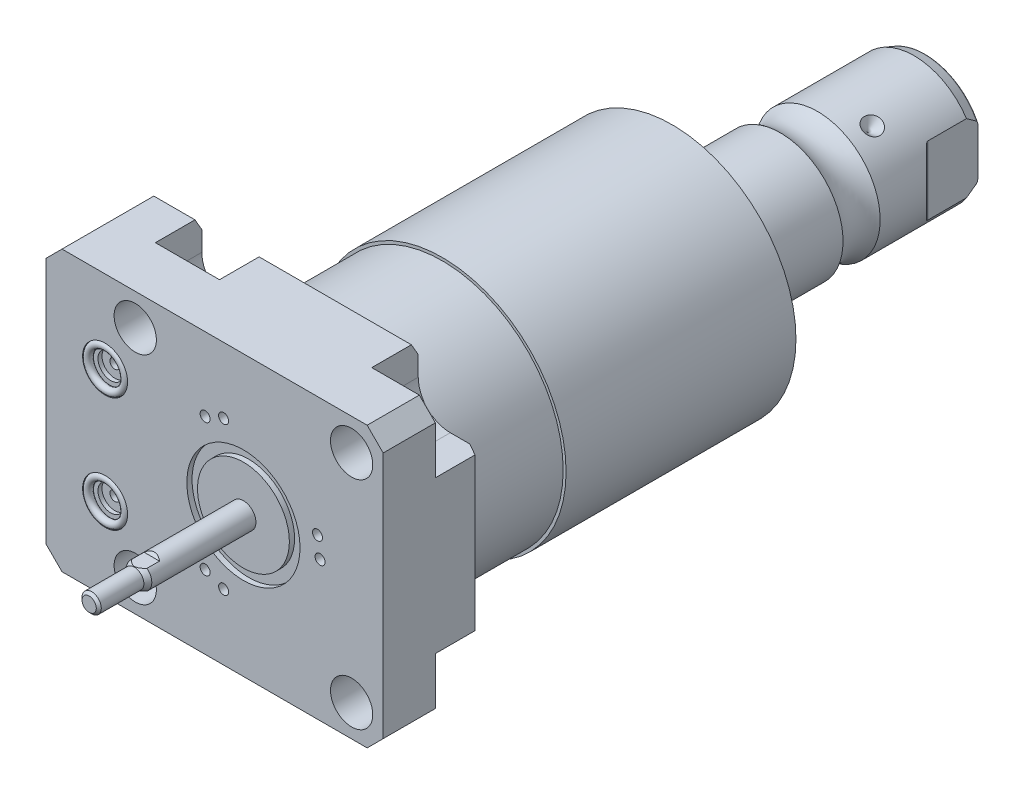
SolidWorks part; units mm, degrees
material "Alloy Steel"
ref_plane "Front Plane" through (0, 0, 0) normal (0, 0, 1) x (1, 0, 0)
ref_plane "Top Plane" through (0, 0, 0) normal (0, 1, 0) x (1, 0, 0)
ref_plane "Right Plane" through (0, 0, 0) normal (1, 0, 0) x (0, 0, -1)
sketch "Sketch1" plane through (0, 0, 0) normal (0, 0, 1) x (1, 0, 0)
  line L0 (-50.063, 35.433) -> (35.433, 35.433)
  line L1 (35.433, 35.433) -> (35.433, -35.433)
  line L2 (35.433, -35.433) -> (-50.063, -35.433)
  line L3 (-50.063, -35.433) -> (-50.063, 35.433)
  dimension "D1" = 85.496
  dimension "D2" = 70.866
  dimension "D3" = 35.433
  dimension "D4" = 35.433
extrude "Extrude1" add sketch "Sketch1" along normal blind 25.019
hole_wizard "Hole1" positions "Sketch22" profile "Sketch21" legacy end condition through all
sketch "Sketch22" plane through (0, 0, 0) normal (0, 0, -1) x (-1, 0, 0)
  line L0 (0, 0) -> (42.7441, 0) construction
  line L1 (0, 0.8532) -> (0, 27.5062) construction
  point P0 (-27.432, -27.432)
  point P9 (-27.432, 27.432)
  point P11 (27.432, 27.432)
  point P12 (27.432, -27.432)
  dimension "D1" = 27.432
  dimension "D2" = 27.432
sketch "Sketch21" plane through (27.432, -27.432, 0) normal (1, 0, 0) x (0, 1, 0)
  line L0 (0, 0) -> (0, 25.019)
  line L1 (0, 25.019) -> (5.3595, 25.019)
  line L2 (5.3595, 25.019) -> (5.3595, 0)
  line L3 (5.3595, 0) -> (0, 0)
  line L4 (0, 110) -> (0, -10) construction
  dimension "Diameter" = 10.719
  dimension "Depth" = 25.019
sketch "Sketch3" plane through (0, 0, 0) normal (0, 0, -1) x (-1, 0, 0)
  line L0 (-27.432, -19.304) -> (-35.433, -19.304)
  line L1 (-35.433, -35.433) -> (-35.433, -19.304)
  line L2 (-35.433, 19.304) -> (-35.433, 35.433)
  line L3 (-35.433, 19.304) -> (-27.432, 19.304)
  line L4 (-19.304, 27.432) -> (-19.304, 35.433)
  line L5 (-35.433, 35.433) -> (-19.304, 35.433)
  line L6 (19.304, 35.433) -> (19.304, 27.432)
  line L7 (35.56, 27.432) -> (35.56, 35.433)
  line L8 (19.304, 35.433) -> (35.56, 35.433)
  line L9 (35.56, -35.433) -> (19.304, -35.433)
  line L10 (35.56, -35.433) -> (35.56, -27.432)
  line L11 (19.304, -27.432) -> (19.304, -35.433)
  line L12 (-19.304, -35.433) -> (-35.433, -35.433)
  line L13 (-19.304, -35.433) -> (-19.304, -27.432)
  line L14 (-35.433, 35.433) -> (50.063, 35.433) construction
  line L15 (-35.433, -35.433) -> (-35.433, 35.433) construction
  line L16 (50.063, -35.433) -> (-35.433, -35.433) construction
  arc A0 (-19.304, -27.432) -> (-27.432, -19.304) centre (-27.432, -27.432) ccw
  arc A1 (-27.432, 19.304) -> (-19.304, 27.432) centre (-27.432, 27.432) ccw
  arc A2 (19.304, 27.432) -> (35.56, 27.432) centre (27.432, 27.432) ccw
  arc A3 (35.56, -27.432) -> (19.304, -27.432) centre (27.432, -27.432) ccw
  circle A8 centre (-27.432, 27.432) radius 5.3595 construction
  circle A9 centre (-27.432, -27.432) radius 5.3595 construction
  circle A10 centre (27.432, -27.432) radius 5.3595 construction
  circle A11 centre (27.432, 27.432) radius 5.3595 construction
  dimension "D1" = 8.128
extrude "Cut-Extrude2" cut sketch "Sketch3" against normal blind 11.786
ref_plane "Plane16" through (0, 0, 12.522) normal (0, 0, 1) x (1, 0, 0)
sketch "Sketch23" plane through (0, 0, 12.522) normal (0, 0, 1) x (1, 0, 0)
  line L0 (-11.9397, -13.0048) -> (-61.0013, -13.0048) construction
  line L1 (-50.063, -23.749) -> (-49.809, -23.749)
  line L3 (-49.809, -23.749) -> (-49.809, -19.6596)
  line L4 (-49.809, -19.6596) -> (-49.0978, -18.9484)
  line L5 (-49.0978, -18.9484) -> (-35.6358, -18.9484)
  line L6 (-35.6358, -18.9484) -> (-35.6358, -13.0048)
  line L7 (-35.6358, -13.0048) -> (-50.063, -13.0048)
  line L8 (-50.063, -13.0048) -> (-50.063, -23.749)
  line L10 (-50.063, 35.433) -> (-50.063, -35.433) construction
  dimension "D1" = 21.4884
  dimension "D2" = 0.254
  dimension "D3" = 45
  dimension "D4" = 13.3096
  dimension "D5" = 11.8872
  dimension "D6" = 14.1732
  dimension "D7" = 13.0048
revolve "Cut-Revolve5" cut sketch "Sketch23" angle 360 about L0
mirror "Mirror1" about plane through (0, 0, 0) normal (0, 1, 0) of "Cut-Revolve5"
sketch "Sketch6" plane through (0, 0, 25.019) normal (0, 0, 1) x (1, 0, 0)
  line L0 (0, 0) -> (-71.0417, 0) construction
  circle A0 centre (-35.077, -14.529) radius 5.7023
  circle A1 centre (-35.077, 14.529) radius 5.7023
  dimension "D4" = 11.4046
  dimension "D1" = 14.529
  dimension "D2" = 29.058
  dimension "D3" = 35.077
extrude "Cut-Extrude3" cut sketch "Sketch6" against normal blind 1.4478
sketch "Sketch7" plane through (0, 0, 23.5712) normal (0, 0, 1) x (1, 0, 0)
  circle A0 centre (-35.077, 14.529) radius 3.2512
  circle A1 centre (-35.077, -14.529) radius 3.2512
  circle A2 centre (-35.077, 14.529) radius 5.7023 construction
  circle A3 centre (-35.077, -14.529) radius 5.7023 construction
  dimension "D1" = 6.5024
extrude "Cut-Extrude4" cut sketch "Sketch7" against normal blind 1.016
sketch "Sketch8" plane through (0, 0, 22.5552) normal (0, 0, 1) x (1, 0, 0)
  circle A0 centre (-35.077, 14.529) radius 1.2446
  circle A1 centre (-35.077, -14.529) radius 1.2446
  circle A2 centre (-35.077, 14.529) radius 5.7023 construction
  circle A3 centre (-35.077, -14.529) radius 5.7023 construction
  dimension "D1" = 2.4892
extrude "Cut-Extrude5" cut sketch "Sketch8" against normal blind 11.9888
ref_plane "Plane17" through (0, 14.5288, 0) normal (0, 1, 0) x (-1, 0, 0)
sketch "Sketch9" plane through (-41.656, 14.5288, 23.5712) normal (0, 1, 0) x (1, 0, 0)
  line L0 (6.579, -1.9469) -> (6.579, 0.0927) construction
  line L3 (0.8767, 0) -> (12.2813, 0) construction
  line L4 (6.579, 13.0048) -> (6.579, 1.016) construction
  circle A0 centre (11.3542, -0.9271) radius 0.9271
  dimension "D1" = 1.8542
  dimension "D2" = 9.5504
revolve "Revolve1" add sketch "Sketch9" angle 360 about L0
mirror "Mirror2" about plane through (0, 0, 0) normal (0, 1, 0) of bodies 116
chamfer "Chamfer1" distance 4.064 angle 45 4 edges at (35.433, -35.433, 18.4025) (35.433, 35.433, 18.4025) (-50.063, 35.433, 12.5095) (-50.063, -35.433, 12.5095)
chamfer "Chamfer2" distance 3.0226 angle 30 5 edges at (-40.7795, -35.433, 0) (0, -35.433, 0) (35.433, 0, 0) (-40.7795, 35.433, 0) (0, 35.433, 0)
sketch "Sketch24" plane through (0, 0, 0) normal (1, 0, 0) x (0, 0, -1)
  line L0 (0, 0) -> (113.9127, 0) construction
  line L1 (0, 0) -> (0, 30.658)
  line L2 (0, 30.658) -> (25.4, 30.658)
  line L3 (25.4, 30.658) -> (25.4, 31.3945)
  line L4 (25.4, 31.3945) -> (83.6873, 31.3945)
  line L5 (83.6873, 31.3945) -> (86.995, 19.05)
  line L6 (86.995, 19.05) -> (86.995, 0)
  line L7 (86.995, 0) -> (0, 0)
  dimension "D1" = 61.316
  dimension "D2" = 25.4
  dimension "D3" = 62.789
  dimension "D4" = 38.1
  dimension "D5" = 15
  dimension "D6" = 86.995
revolve "Revolve4" add sketch "Sketch24" angle 360 about L0
sketch "Sketch17" plane through (0, 0, 0) normal (1, 0, 0) x (0, 0, -1)
  line L0 (86.995, 0) -> (86.995, -15.875)
  line L1 (86.995, -15.875) -> (111.1417, -15.875)
  line L2 (120.5563, -15.875) -> (145.034, -15.875)
  line L3 (147.955, -14.8118) -> (147.955, 0)
  line L4 (147.955, 0) -> (86.995, 0)
  line L5 (130.8989, 0) -> (0.816, 0) construction
  line L6 (86.995, -19.05) -> (86.995, 19.05) construction
  line L7 (-25.019, -31.369) -> (-25.019, 31.369) construction
  line L8 (147.955, -14.8118) -> (145.034, -15.875)
  arc A0 (120.5563, -15.875) -> (111.1417, -15.875) centre (115.849, -22.2505) ccw
  dimension "D2" = 20
  dimension "D4" = 7.925
  dimension "D5" = 28.651
  dimension "D1" = 172.974
  dimension "D3" = 31.75
  dimension "D6" = 32.106
  dimension "D7" = 2.921
revolve "Revolve3" add sketch "Sketch17" angle 360 about L5
sketch "Sketch30" plane through (0, 0, 0) normal (0, 1, 0) x (1, 0, 0)
  line L0 (-27.8193, 126.517) -> (0.6125, 126.517) construction
  line L1 (-15.875, 128.93) -> (-13.462, 126.517)
  line L2 (-15.875, 145.034) -> (-15.875, 120.5563) construction
  line L3 (-13.462, 126.517) -> (-15.875, 126.517)
  line L4 (-15.875, 126.517) -> (-15.875, 128.93)
  arc A0 (-15.875, 111.1417) -> (-15.875, 120.5563) centre (-22.2505, 115.849) ccw construction
  dimension "D1" = 45
  dimension "D2" = 4.826
  dimension "D3" = 10.668
revolve "Cut-Revolve6" cut sketch "Sketch30" angle 360 about L0
pattern_circular "CirPattern1" count 3 over 360 about axis through (0, 0, -130.8989) along (0, 0, -1) of "Cut-Revolve6"
fillet "Fillet2" radius 0.635 1 edges at (-14.8118, 0, -147.955)
sketch "Sketch32" plane through (0, 0, 0) normal (0, 1, 0) x (1, 0, 0)
  line L0 (0, 0) -> (0, 187.7199) construction
  line L1 (-13.284, 147.955) -> (-13.284, 135.255)
  line L2 (14.3672, 147.955) -> (-14.3672, 147.955) construction
  line L3 (-13.5072, 134.7162) -> (-15.875, 132.3484)
  line L4 (-15.875, 145.034) -> (-15.875, 128.93) construction
  line L5 (-15.875, 132.3484) -> (-15.875, 147.955)
  line L6 (-15.875, 147.955) -> (-13.284, 147.955)
  line L7 (15.875, 147.955) -> (13.284, 147.955)
  line L8 (15.875, 132.3484) -> (15.875, 147.955)
  line L9 (13.5072, 134.7162) -> (15.875, 132.3484)
  line L10 (13.284, 147.955) -> (13.284, 135.255)
  arc A0 (-13.284, 135.255) -> (-13.5072, 134.7162) centre (-14.046, 135.255) cw
  arc A1 (13.284, 135.255) -> (13.5072, 134.7162) centre (14.046, 135.255) ccw
  dimension "D1" = 0.762
  dimension "D2" = 12.7
  dimension "D3" = 45
  dimension "D4" = 26.568
extrude "Cut-Extrude8" cut sketch "Sketch32" against normal through all and the other way through all
hole_wizard "Hole2" positions "Sketch34" profile "Sketch33" legacy
sketch "Sketch34" plane through (0, 0, -147.955) normal (0, 0, -1) x (-1, 0, 0)
  circle A0 centre (0, 0) radius 15.875 construction
  point P0 (0, 0)
sketch "Sketch33" plane through (0, 0, -147.955) normal (1, 0, 0) x (0, 1, 0)
  line L0 (0, 0) -> (0, 29.5665)
  line L1 (0, 29.5665) -> (6.9342, 25.4)
  line L2 (6.9342, 25.4) -> (6.9342, 0)
  line L4 (6.9342, 0) -> (0, 0)
  line L6 (0, 29.5665) -> (-6.9342, 25.4) construction
  line L7 (0, -4.2442) -> (0, 117.3081) construction
  dimension "Diameter" = 13.8684
  dimension "Depth" = 25.4
  dimension "Drill Angle" = 118
sketch "Sketch35" plane through (0, 0, 0) normal (1, 0, 0) x (0, 0, -1)
  line L0 (-1000, 0) -> (49000, 0) construction
  line L1 (-25.019, 0) -> (-25.019, -3.175)
  line L2 (-25.019, -31.369) -> (-25.019, 31.369) construction
  line L3 (-25.019, -3.175) -> (-51.4296, -3.175)
  line L4 (-51.4296, -3.175) -> (-52.7054, -2.4384)
  line L5 (-52.7054, -2.4384) -> (-63.5004, -2.4384)
  line L6 (-63.5004, -2.4384) -> (-64.1354, -1.8034)
  line L7 (-64.1354, -1.8034) -> (-64.1354, 0)
  line L8 (-64.1354, 0) -> (-25.019, 0)
  line L9 (147.955, -14.3672) -> (147.955, -5.4728) construction
  dimension "D1" = 45
  dimension "D2" = 4.8768
  dimension "D3" = 30
  dimension "D4" = 6.35
  dimension "D5" = 11.43
  dimension "D6" = 212.0904
  dimension "D7" = 0.635
revolve "Revolve5" add sketch "Sketch35" angle 360 about L0
sketch "Sketch36" plane through (0, 0, 0) normal (1, 0, 0) x (0, 0, -1)
  line L0 (-1000, 0) -> (49000, 0) construction
  line L1 (-47.5873, -3.175) -> (-48.2604, -2.5019)
  line L2 (-51.4296, -3.175) -> (-25.019, -3.175) construction
  line L3 (-48.2604, -2.5019) -> (-64.1354, -2.5019)
  line L4 (-64.1354, 1.8034) -> (-64.1354, -1.8034) construction
  line L5 (-47.5873, -3.175) -> (-64.1354, -3.175)
  line L6 (-64.1354, -3.175) -> (-64.1354, -2.5019)
  line L7 (-47.5873, 3.175) -> (-48.2604, 2.5019)
  line L8 (-48.2604, 2.5019) -> (-64.1354, 2.5019)
  line L9 (-47.5873, 3.175) -> (-64.1354, 3.175)
  line L10 (-64.1354, 3.175) -> (-64.1354, 2.5019)
  dimension "D1" = 5.0038
  dimension "D2" = 45
  dimension "D3" = 15.875
extrude "Cut-Extrude9" cut sketch "Sketch36" against normal mid plane 7.62
sketch "Sketch37" plane through (0, 0, 0) normal (1, 0, 0) x (0, 0, -1)
  line L0 (-1000, 0) -> (49000, 0) construction
  line L1 (-25.019, -31.369) -> (-25.019, 31.369) construction
  line L2 (-25.019, -11.6459) -> (-23.6982, -11.6459)
  line L3 (-25.019, -11.6459) -> (-25.019, -14.351)
  line L4 (-25.019, -14.351) -> (-23.6982, -14.351)
  line L5 (-23.6982, -11.6459) -> (-23.6982, -14.351)
  dimension "D1" = 1.3208
  dimension "D2" = 23.2918
  dimension "D3" = 28.7021
revolve "Cut-Revolve7" cut sketch "Sketch37" angle 360 about L0
sketch "Sketch38" plane through (0, 0, 25.019) normal (0, 0, 1) x (1, 0, 0)
  line L0 (-1000, 0) -> (49000, 0) construction
  line L1 (0, 0) -> (48296.2913, 12940.9523) construction
  line L2 (0, 0) -> (25000, 43301.2702) construction
  circle A0 centre (0, 0) radius 19.431 construction
  circle A1 centre (19.431, 0) radius 1.27
  circle A2 centre (18.7689, 5.0291) radius 1.27
  circle A3 centre (-5.0291, 18.7689) radius 1.27
  circle A4 centre (-9.7155, 16.8278) radius 1.27
  circle A5 centre (-5.0291, -18.7689) radius 1.27
  circle A6 centre (-9.7155, -16.8278) radius 1.27
  dimension "D3" = 38.8621
  dimension "D4" = 2.54
  dimension "D5" = 2.54
  dimension "D1" = 15
  dimension "D2" = 60
extrude "Cut-Extrude10" cut sketch "Sketch38" against normal blind 7.62
